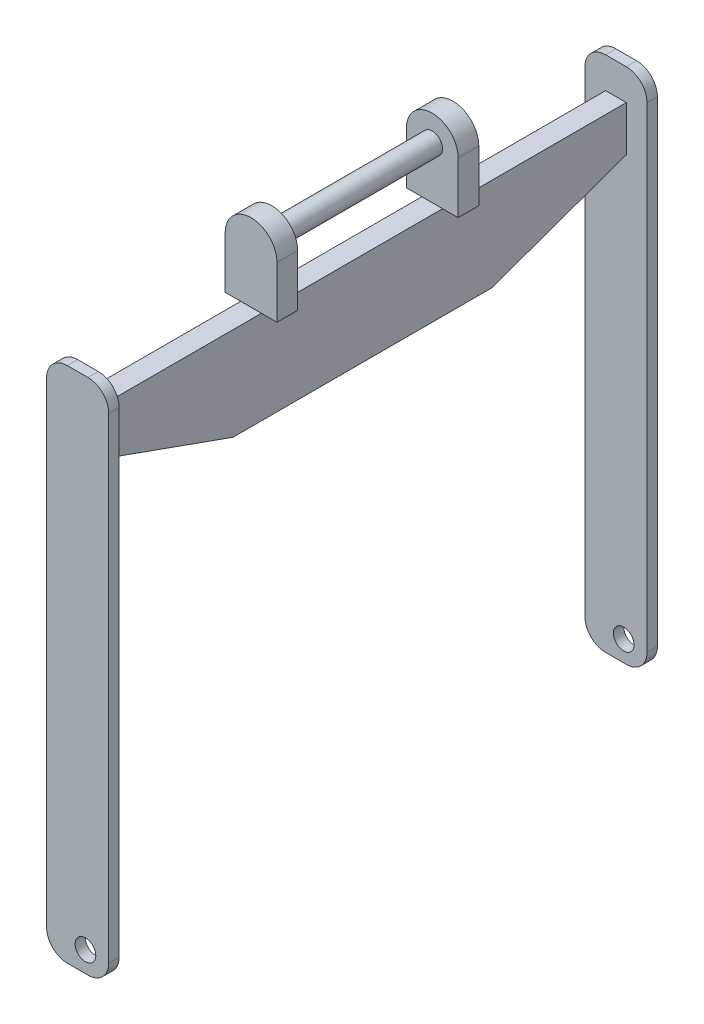
SolidWorks part; units mm, degrees
ref_plane "Front Plane" through (0, 0, 0) normal (0, 0, 1) x (1, 0, 0)
ref_plane "Top Plane" through (0, 0, 0) normal (0, 1, 0) x (1, 0, 0)
ref_plane "Right Plane" through (0, 0, 0) normal (1, 0, 0) x (0, 0, -1)
sketch "Sketch1" plane through (0, 0, 0) normal (0, 0, 1) x (1, 0, 0)
  circle A0 centre (0, 0) radius 10
  dimension "D1" = 20
extrude "Boss-Extrude1" add sketch "Sketch1" along normal mid plane 195
sketch "Sketch2" plane through (0, 0, 97.5) normal (0, 0, 1) x (1, 0, 0)
  line L0 (-25, 0) -> (-25, -50)
  line L1 (-25, -50) -> (25, -50)
  line L2 (25, -50) -> (25, 0)
  arc A0 (25, 0) -> (-25, 0) centre (0, 0) ccw
  dimension "D1" = 50
  dimension "D2" = 50
extrude "Boss-Extrude2" add sketch "Sketch2" against normal blind 20 separate body
mirror "Mirror1" about plane through (0, 0, 0) normal (0, 0, 1) of "Boss-Extrude1"
mirror "Mirror3" about plane through (0, 0, 0) normal (0, 0, 1) of "Boss-Extrude2"
sketch "Sketch3" plane through (0, 0, 0) normal (1, 0, 0) x (0, 0, -1)
  line L0 (0, 0) -> (0, -50) construction
  line L1 (-265, -50) -> (265, -50)
  line L2 (-77.5, -50) -> (-97.5, -50) construction
  line L3 (-265, -50) -> (-265, -90)
  line L4 (-265, -90) -> (-125, -140)
  line L5 (-125, -140) -> (125, -140)
  line L6 (125, -140) -> (265, -90)
  line L7 (265, -90) -> (265, -50)
  line L8 (0, -50) -> (0, -140) construction
  dimension "D1" = 530
  dimension "D2" = 40
  dimension "D3" = 90
  dimension "D4" = 250
extrude "Boss-Extrude3" add sketch "Sketch3" along normal mid plane 20
sketch "Sketch4" plane through (0, 0, -265) normal (0, 0, -1) x (-1, 0, 0)
  line L0 (0, 0) -> (0, -20) construction
  line L1 (-30, -20) -> (30, -20)
  line L2 (-30, -20) -> (-30, -520)
  line L3 (-30, -520) -> (30, -520)
  line L4 (30, -20) -> (30, -520)
  dimension "D1" = 20
  dimension "D2" = 60
  dimension "D3" = 500
extrude "Boss-Extrude4" add sketch "Sketch4" against normal blind 10 separate body
fillet "Fillet1" radius 20 4 edges at (30, -520, -260) (-30, -520, -260) (-30, -20, -260) (30, -20, -260)
mirror "Mirror6" about plane through (0, 0, 0) normal (0, 0, 1) of bodies 106
sketch "Sketch5" plane through (0, 0, -265) normal (0, 0, -1) x (-1, 0, 0)
  line L0 (-30, -40) -> (-30, -500) construction
  circle A0 centre (-7.5, -500) radius 10
  dimension "D1" = 20
  dimension "D2" = 22.5
extrude "Cut-Extrude1" cut sketch "Sketch5" against normal through all
